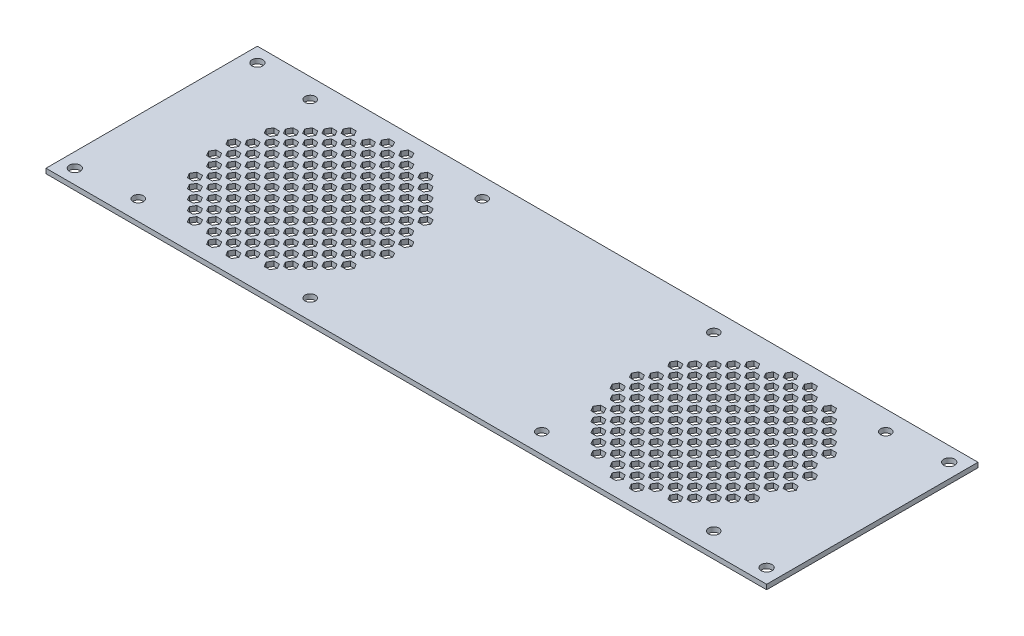
SolidWorks part; units mm, degrees
ref_plane "Front Plane" through (0, 0, 0) normal (0, 0, 1) x (1, 0, 0)
ref_plane "Top Plane" through (0, 0, 0) normal (0, 1, 0) x (1, 0, 0)
ref_plane "Right Plane" through (0, 0, 0) normal (1, 0, 0) x (0, 0, -1)
sketch "Sketch1" plane through (0, 0, 0) normal (0, 1, 0) x (1, 0, 0)
  line L1 (0, 0) -> (300, 0)
  line L2 (0, 0) -> (0, 88)
  line L3 (0, 88) -> (300, 88)
  line L4 (300, 0) -> (300, 88)
  dimension "D1" = 88
  dimension "D2" = 300
extrude "Boss-Extrude1" add sketch "Sketch1" along normal blind 2
hole_wizard "M4 Clearance Hole1" positions "Sketch2" profile "Sketch3" hole size "M4" standard "DIN" end condition up to next
sketch "Sketch2" plane through (0, 2, 0) normal (0, 1, 0) x (1, 0, 0)
  line L0 (0, 88) -> (0, 0) construction
  line L1 (0, 0) -> (300, 0) construction
  line L2 (300, 88) -> (0, 88) construction
  line L3 (300, 0) -> (300, 88) construction
  point P0 (294, 6)
  point P2 (294, 82)
  point P4 (6, 82)
  point P6 (6, 6)
  dimension "D1" = 6
  dimension "D2" = 6
  dimension "D3" = 6
  dimension "D4" = 6
sketch "Sketch3" plane through (294, 2, -6) normal (1, 0, 0) x (0, 0, 1)
  line L0 (0, 0) -> (0, 2)
  line L1 (0, 2) -> (2.25, 2)
  line L2 (2.25, 2) -> (2.25, 0)
  line L5 (2.25, 0) -> (0, 0)
  line L11 (0, -6.35) -> (0, 107.95) construction
  dimension "Thru Hole Dia." = 4.5
  dimension "Thru Hole Depth" = 2
sketch "Sketch4" plane through (0, 2, 0) normal (0, 1, 0) x (1, 0, 0)
  line L0 (0, 88) -> (0, 0) construction
  line L1 (68.3094, 44) -> (67.1547, 46)
  line L2 (67.1547, 46) -> (64.8453, 46)
  line L3 (64.8453, 46) -> (63.6906, 44)
  line L4 (63.6906, 44) -> (64.8453, 42)
  line L5 (64.8453, 42) -> (67.1547, 42)
  line L6 (67.1547, 42) -> (68.3094, 44)
  line L7 (76.3094, 44) -> (75.1547, 46)
  line L8 (75.1547, 46) -> (72.8453, 46)
  line L9 (72.8453, 46) -> (71.6906, 44)
  line L10 (71.6906, 44) -> (72.8453, 42)
  line L11 (72.8453, 42) -> (75.1547, 42)
  line L12 (75.1547, 42) -> (76.3094, 44)
  line L13 (84.3094, 44) -> (83.1547, 46)
  line L14 (83.1547, 46) -> (80.8453, 46)
  line L15 (80.8453, 46) -> (79.6906, 44)
  line L16 (79.6906, 44) -> (80.8453, 42)
  line L17 (80.8453, 42) -> (83.1547, 42)
  line L18 (83.1547, 42) -> (84.3094, 44)
  line L19 (92.3094, 44) -> (91.1547, 46)
  line L20 (91.1547, 46) -> (88.8453, 46)
  line L21 (88.8453, 46) -> (87.6906, 44)
  line L22 (87.6906, 44) -> (88.8453, 42)
  line L23 (88.8453, 42) -> (91.1547, 42)
  line L24 (91.1547, 42) -> (92.3094, 44)
  line L25 (100.3094, 44) -> (99.1547, 46)
  line L26 (99.1547, 46) -> (96.8453, 46)
  line L27 (96.8453, 46) -> (95.6906, 44)
  line L28 (95.6906, 44) -> (96.8453, 42)
  line L29 (96.8453, 42) -> (99.1547, 42)
  line L30 (99.1547, 42) -> (100.3094, 44)
  line L31 (76.3094, 52) -> (75.1547, 54)
  line L32 (75.1547, 54) -> (72.8453, 54)
  line L33 (72.8453, 54) -> (71.6906, 52)
  line L34 (71.6906, 52) -> (72.8453, 50)
  line L35 (72.8453, 50) -> (75.1547, 50)
  line L36 (75.1547, 50) -> (76.3094, 52)
  line L37 (84.3094, 52) -> (83.1547, 54)
  line L38 (83.1547, 54) -> (80.8453, 54)
  line L39 (80.8453, 54) -> (79.6906, 52)
  line L40 (79.6906, 52) -> (80.8453, 50)
  line L41 (80.8453, 50) -> (83.1547, 50)
  line L42 (83.1547, 50) -> (84.3094, 52)
  line L43 (92.3094, 52) -> (91.1547, 54)
  line L44 (91.1547, 54) -> (88.8453, 54)
  line L45 (88.8453, 54) -> (87.6906, 52)
  line L46 (87.6906, 52) -> (88.8453, 50)
  line L47 (88.8453, 50) -> (91.1547, 50)
  line L48 (91.1547, 50) -> (92.3094, 52)
  line L49 (100.3094, 52) -> (99.1547, 54)
  line L50 (99.1547, 54) -> (96.8453, 54)
  line L51 (96.8453, 54) -> (95.6906, 52)
  line L52 (95.6906, 52) -> (96.8453, 50)
  line L53 (96.8453, 50) -> (99.1547, 50)
  line L54 (99.1547, 50) -> (100.3094, 52)
  line L55 (76.3094, 60) -> (75.1547, 62)
  line L56 (75.1547, 62) -> (72.8453, 62)
  line L57 (72.8453, 62) -> (71.6906, 60)
  line L58 (71.6906, 60) -> (72.8453, 58)
  line L59 (72.8453, 58) -> (75.1547, 58)
  line L60 (75.1547, 58) -> (76.3094, 60)
  line L61 (84.3094, 60) -> (83.1547, 62)
  line L62 (83.1547, 62) -> (80.8453, 62)
  line L63 (80.8453, 62) -> (79.6906, 60)
  line L64 (79.6906, 60) -> (80.8453, 58)
  line L65 (80.8453, 58) -> (83.1547, 58)
  line L66 (83.1547, 58) -> (84.3094, 60)
  line L67 (92.3094, 60) -> (91.1547, 62)
  line L68 (91.1547, 62) -> (88.8453, 62)
  line L69 (88.8453, 62) -> (87.6906, 60)
  line L70 (87.6906, 60) -> (88.8453, 58)
  line L71 (88.8453, 58) -> (91.1547, 58)
  line L72 (91.1547, 58) -> (92.3094, 60)
  line L73 (100.3094, 60) -> (99.1547, 62)
  line L74 (99.1547, 62) -> (96.8453, 62)
  line L75 (96.8453, 62) -> (95.6906, 60)
  line L76 (95.6906, 60) -> (96.8453, 58)
  line L77 (96.8453, 58) -> (99.1547, 58)
  line L78 (99.1547, 58) -> (100.3094, 60)
  line L79 (76.3094, 68) -> (75.1547, 70)
  line L80 (75.1547, 70) -> (72.8453, 70)
  line L81 (72.8453, 70) -> (71.6906, 68)
  line L82 (71.6906, 68) -> (72.8453, 66)
  line L83 (72.8453, 66) -> (75.1547, 66)
  line L84 (75.1547, 66) -> (76.3094, 68)
  line L85 (84.3094, 68) -> (83.1547, 70)
  line L86 (83.1547, 70) -> (80.8453, 70)
  line L87 (80.8453, 70) -> (79.6906, 68)
  line L88 (79.6906, 68) -> (80.8453, 66)
  line L89 (80.8453, 66) -> (83.1547, 66)
  line L90 (83.1547, 66) -> (84.3094, 68)
  line L91 (92.3094, 68) -> (91.1547, 70)
  line L92 (91.1547, 70) -> (88.8453, 70)
  line L93 (88.8453, 70) -> (87.6906, 68)
  line L94 (87.6906, 68) -> (88.8453, 66)
  line L95 (88.8453, 66) -> (91.1547, 66)
  line L96 (91.1547, 66) -> (92.3094, 68)
  line L103 (76.3094, 76) -> (75.1547, 78)
  line L104 (75.1547, 78) -> (72.8453, 78)
  line L105 (72.8453, 78) -> (71.6906, 76)
  line L106 (71.6906, 76) -> (72.8453, 74)
  line L107 (72.8453, 74) -> (75.1547, 74)
  line L108 (75.1547, 74) -> (76.3094, 76)
  line L109 (84.3094, 76) -> (83.1547, 78)
  line L110 (83.1547, 78) -> (80.8453, 78)
  line L111 (80.8453, 78) -> (79.6906, 76)
  line L112 (79.6906, 76) -> (80.8453, 74)
  line L113 (80.8453, 74) -> (83.1547, 74)
  line L114 (83.1547, 74) -> (84.3094, 76)
  line L127 (68.3094, 52) -> (67.1547, 54)
  line L128 (67.1547, 54) -> (64.8453, 54)
  line L129 (64.8453, 54) -> (63.6906, 52)
  line L130 (63.6906, 52) -> (64.8453, 50)
  line L131 (64.8453, 50) -> (67.1547, 50)
  line L132 (67.1547, 50) -> (68.3094, 52)
  line L133 (68.3094, 60) -> (67.1547, 62)
  line L134 (67.1547, 62) -> (64.8453, 62)
  line L135 (64.8453, 62) -> (63.6906, 60)
  line L136 (63.6906, 60) -> (64.8453, 58)
  line L137 (64.8453, 58) -> (67.1547, 58)
  line L138 (67.1547, 58) -> (68.3094, 60)
  line L139 (68.3094, 68) -> (67.1547, 70)
  line L140 (67.1547, 70) -> (64.8453, 70)
  line L141 (64.8453, 70) -> (63.6906, 68)
  line L142 (63.6906, 68) -> (64.8453, 66)
  line L143 (64.8453, 66) -> (67.1547, 66)
  line L144 (67.1547, 66) -> (68.3094, 68)
  line L145 (68.3094, 76) -> (67.1547, 78)
  line L146 (67.1547, 78) -> (64.8453, 78)
  line L147 (64.8453, 78) -> (63.6906, 76)
  line L148 (63.6906, 76) -> (64.8453, 74)
  line L149 (64.8453, 74) -> (67.1547, 74)
  line L150 (67.1547, 74) -> (68.3094, 76)
  line L151 (92.3094, 76) -> (91.1547, 78) [skipped]
  line L152 (91.1547, 78) -> (88.8453, 78) [skipped]
  line L153 (88.8453, 78) -> (87.6906, 76) [skipped]
  line L154 (87.6906, 76) -> (88.8453, 74) [skipped]
  line L155 (88.8453, 74) -> (91.1547, 74) [skipped]
  line L156 (91.1547, 74) -> (92.3094, 76) [skipped]
  line L157 (100.3094, 76) -> (99.1547, 78) [skipped]
  line L158 (99.1547, 78) -> (96.8453, 78) [skipped]
  line L159 (96.8453, 78) -> (95.6906, 76) [skipped]
  line L160 (95.6906, 76) -> (96.8453, 74) [skipped]
  line L161 (96.8453, 74) -> (99.1547, 74) [skipped]
  line L162 (99.1547, 74) -> (100.3094, 76) [skipped]
  line L163 (100.3094, 68) -> (99.1547, 70) [skipped]
  line L164 (99.1547, 70) -> (96.8453, 70) [skipped]
  line L165 (96.8453, 70) -> (95.6906, 68) [skipped]
  line L166 (95.6906, 68) -> (96.8453, 66) [skipped]
  line L167 (96.8453, 66) -> (99.1547, 66) [skipped]
  line L168 (99.1547, 66) -> (100.3094, 68) [skipped]
  circle A0 centre (66, 44) radius 2 construction
  point P11 (0, 44)
  dimension "D2" = 4
  dimension "D1" = 66
  dimension "D5" = 8
  dimension "D6" = 8
  dimension "D3" = 5
  dimension "D4" = 5
extrude "Cut-Extrude1" cut sketch "Sketch4" against normal up to next (2 mm away)
sketch "Sketch5" plane through (0, 2, 0) normal (0, 1, 0) x (1, 0, 0)
  line L0 (67.1547, 46) -> (64.8453, 46) construction
  line L1 (72.3094, 48) -> (71.1547, 50)
  line L2 (71.1547, 50) -> (68.8453, 50)
  line L3 (68.8453, 50) -> (67.6906, 48)
  line L4 (67.6906, 48) -> (68.8453, 46)
  line L5 (68.8453, 46) -> (71.1547, 46)
  line L6 (71.1547, 46) -> (72.3094, 48)
  line L7 (64.8453, 42) -> (67.1547, 42) construction
  line L8 (80.3094, 48) -> (79.1547, 50)
  line L9 (79.1547, 50) -> (76.8453, 50)
  line L10 (76.8453, 50) -> (75.6906, 48)
  line L11 (75.6906, 48) -> (76.8453, 46)
  line L12 (76.8453, 46) -> (79.1547, 46)
  line L13 (79.1547, 46) -> (80.3094, 48)
  line L14 (88.3094, 48) -> (87.1547, 50)
  line L15 (87.1547, 50) -> (84.8453, 50)
  line L16 (84.8453, 50) -> (83.6906, 48)
  line L17 (83.6906, 48) -> (84.8453, 46)
  line L18 (84.8453, 46) -> (87.1547, 46)
  line L19 (87.1547, 46) -> (88.3094, 48)
  line L20 (96.3094, 48) -> (95.1547, 50)
  line L21 (95.1547, 50) -> (92.8453, 50)
  line L22 (92.8453, 50) -> (91.6906, 48)
  line L23 (91.6906, 48) -> (92.8453, 46)
  line L24 (92.8453, 46) -> (95.1547, 46)
  line L25 (95.1547, 46) -> (96.3094, 48)
  line L26 (104.3094, 48) -> (103.1547, 50)
  line L27 (103.1547, 50) -> (100.8453, 50)
  line L28 (100.8453, 50) -> (99.6906, 48)
  line L29 (99.6906, 48) -> (100.8453, 46)
  line L30 (100.8453, 46) -> (103.1547, 46)
  line L31 (103.1547, 46) -> (104.3094, 48)
  line L32 (80.3094, 56) -> (79.1547, 58)
  line L33 (79.1547, 58) -> (76.8453, 58)
  line L34 (76.8453, 58) -> (75.6906, 56)
  line L35 (75.6906, 56) -> (76.8453, 54)
  line L36 (76.8453, 54) -> (79.1547, 54)
  line L37 (79.1547, 54) -> (80.3094, 56)
  line L38 (88.3094, 56) -> (87.1547, 58)
  line L39 (87.1547, 58) -> (84.8453, 58)
  line L40 (84.8453, 58) -> (83.6906, 56)
  line L41 (83.6906, 56) -> (84.8453, 54)
  line L42 (84.8453, 54) -> (87.1547, 54)
  line L43 (87.1547, 54) -> (88.3094, 56)
  line L44 (96.3094, 56) -> (95.1547, 58)
  line L45 (95.1547, 58) -> (92.8453, 58)
  line L46 (92.8453, 58) -> (91.6906, 56)
  line L47 (91.6906, 56) -> (92.8453, 54)
  line L48 (92.8453, 54) -> (95.1547, 54)
  line L49 (95.1547, 54) -> (96.3094, 56)
  line L56 (80.3094, 64) -> (79.1547, 66)
  line L57 (79.1547, 66) -> (76.8453, 66)
  line L58 (76.8453, 66) -> (75.6906, 64)
  line L59 (75.6906, 64) -> (76.8453, 62)
  line L60 (76.8453, 62) -> (79.1547, 62)
  line L61 (79.1547, 62) -> (80.3094, 64)
  line L62 (88.3094, 64) -> (87.1547, 66)
  line L63 (87.1547, 66) -> (84.8453, 66)
  line L64 (84.8453, 66) -> (83.6906, 64)
  line L65 (83.6906, 64) -> (84.8453, 62)
  line L66 (84.8453, 62) -> (87.1547, 62)
  line L67 (87.1547, 62) -> (88.3094, 64)
  line L68 (96.3094, 64) -> (95.1547, 66)
  line L69 (95.1547, 66) -> (92.8453, 66)
  line L70 (92.8453, 66) -> (91.6906, 64)
  line L71 (91.6906, 64) -> (92.8453, 62)
  line L72 (92.8453, 62) -> (95.1547, 62)
  line L73 (95.1547, 62) -> (96.3094, 64)
  line L80 (80.3094, 72) -> (79.1547, 74)
  line L81 (79.1547, 74) -> (76.8453, 74)
  line L82 (76.8453, 74) -> (75.6906, 72)
  line L83 (75.6906, 72) -> (76.8453, 70)
  line L84 (76.8453, 70) -> (79.1547, 70)
  line L85 (79.1547, 70) -> (80.3094, 72)
  line L86 (88.3094, 72) -> (87.1547, 74)
  line L87 (87.1547, 74) -> (84.8453, 74)
  line L88 (84.8453, 74) -> (83.6906, 72)
  line L89 (83.6906, 72) -> (84.8453, 70)
  line L90 (84.8453, 70) -> (87.1547, 70)
  line L91 (87.1547, 70) -> (88.3094, 72)
  line L128 (72.3094, 56) -> (71.1547, 58)
  line L129 (71.1547, 58) -> (68.8453, 58)
  line L130 (68.8453, 58) -> (67.6906, 56)
  line L131 (67.6906, 56) -> (68.8453, 54)
  line L132 (68.8453, 54) -> (71.1547, 54)
  line L133 (71.1547, 54) -> (72.3094, 56)
  line L134 (72.3094, 64) -> (71.1547, 66)
  line L135 (71.1547, 66) -> (68.8453, 66)
  line L136 (68.8453, 66) -> (67.6906, 64)
  line L137 (67.6906, 64) -> (68.8453, 62)
  line L138 (68.8453, 62) -> (71.1547, 62)
  line L139 (71.1547, 62) -> (72.3094, 64)
  line L140 (72.3094, 72) -> (71.1547, 74)
  line L141 (71.1547, 74) -> (68.8453, 74)
  line L142 (68.8453, 74) -> (67.6906, 72)
  line L143 (67.6906, 72) -> (68.8453, 70)
  line L144 (68.8453, 70) -> (71.1547, 70)
  line L145 (71.1547, 70) -> (72.3094, 72)
  line L146 (72.3094, 80) -> (71.1547, 82)
  line L147 (71.1547, 82) -> (68.8453, 82)
  line L148 (68.8453, 82) -> (67.6906, 80)
  line L149 (67.6906, 80) -> (68.8453, 78)
  line L150 (68.8453, 78) -> (71.1547, 78)
  line L151 (71.1547, 78) -> (72.3094, 80)
  line L152 (96.3094, 72) -> (95.1547, 74) [skipped]
  line L153 (95.1547, 74) -> (92.8453, 74) [skipped]
  line L154 (92.8453, 74) -> (91.6906, 72) [skipped]
  line L155 (91.6906, 72) -> (92.8453, 70) [skipped]
  line L156 (92.8453, 70) -> (95.1547, 70) [skipped]
  line L157 (95.1547, 70) -> (96.3094, 72) [skipped]
  line L158 (103.1547, 70) -> (104.3094, 72) [skipped]
  line L159 (104.3094, 72) -> (103.1547, 74) [skipped]
  line L160 (103.1547, 74) -> (100.8453, 74) [skipped]
  line L161 (100.8453, 74) -> (99.6906, 72) [skipped]
  line L162 (99.6906, 72) -> (100.8453, 70) [skipped]
  line L163 (100.8453, 70) -> (103.1547, 70) [skipped]
  line L164 (104.3094, 80) -> (103.1547, 82) [skipped]
  line L165 (103.1547, 82) -> (100.8453, 82) [skipped]
  line L166 (100.8453, 82) -> (99.6906, 80) [skipped]
  line L167 (99.6906, 80) -> (100.8453, 78) [skipped]
  line L168 (100.8453, 78) -> (103.1547, 78) [skipped]
  line L169 (103.1547, 78) -> (104.3094, 80) [skipped]
  line L170 (96.3094, 80) -> (95.1547, 82) [skipped]
  line L171 (95.1547, 82) -> (92.8453, 82) [skipped]
  line L172 (92.8453, 82) -> (91.6906, 80) [skipped]
  line L173 (91.6906, 80) -> (92.8453, 78) [skipped]
  line L174 (92.8453, 78) -> (95.1547, 78) [skipped]
  line L175 (95.1547, 78) -> (96.3094, 80) [skipped]
  line L176 (104.3094, 64) -> (103.1547, 66) [skipped]
  line L177 (103.1547, 66) -> (100.8453, 66) [skipped]
  line L178 (100.8453, 66) -> (99.6906, 64) [skipped]
  line L179 (99.6906, 64) -> (100.8453, 62) [skipped]
  line L180 (100.8453, 62) -> (103.1547, 62) [skipped]
  line L181 (103.1547, 62) -> (104.3094, 64) [skipped]
  line L182 (104.3094, 56) -> (103.1547, 58) [skipped]
  line L183 (103.1547, 58) -> (100.8453, 58) [skipped]
  line L184 (100.8453, 58) -> (99.6906, 56) [skipped]
  line L185 (99.6906, 56) -> (100.8453, 54) [skipped]
  line L186 (100.8453, 54) -> (103.1547, 54) [skipped]
  line L187 (103.1547, 54) -> (104.3094, 56) [skipped]
  line L188 (88.3094, 80) -> (87.1547, 82) [skipped]
  line L189 (87.1547, 82) -> (84.8453, 82) [skipped]
  line L190 (84.8453, 82) -> (83.6906, 80) [skipped]
  line L191 (83.6906, 80) -> (84.8453, 78) [skipped]
  line L192 (84.8453, 78) -> (87.1547, 78) [skipped]
  line L193 (87.1547, 78) -> (88.3094, 80) [skipped]
  line L194 (80.3094, 80) -> (79.1547, 82) [skipped]
  line L195 (79.1547, 82) -> (76.8453, 82) [skipped]
  line L196 (76.8453, 82) -> (75.6906, 80) [skipped]
  line L197 (75.6906, 80) -> (76.8453, 78) [skipped]
  line L198 (76.8453, 78) -> (79.1547, 78) [skipped]
  line L199 (79.1547, 78) -> (80.3094, 80) [skipped]
  circle A0 centre (70, 48) radius 2 construction
  point P13 (66, 42)
  dimension "D1" = 4
  dimension "D2" = 4
  dimension "D5" = 8
  dimension "D6" = 8
  dimension "D3" = 5
  dimension "D4" = 5
extrude "Cut-Extrude2" cut sketch "Sketch5" against normal up to next (2 mm away)
ref_plane "Plane1" through (66, 0, 0) normal (-1, 0, 0) x (0, 0, 1)
ref_plane "Plane2" through (0, 0, -44) normal (0, 0, -1) x (-1, 0, 0)
mirror "Mirror1" about plane through (66, 0, 0) normal (-1, 0, 0) of "Cut-Extrude2", "Cut-Extrude1"
mirror "Mirror2" about plane through (0, 0, -44) normal (0, 0, -1) of "Mirror1", "Cut-Extrude1", "Cut-Extrude2"
ref_plane "Plane3" through (150, 0, 0) normal (-1, 0, 0) x (0, 0, 1)
mirror "Mirror3" about plane through (150, 0, 0) normal (-1, 0, 0) of "Mirror2", "Cut-Extrude1", "Cut-Extrude2", "Mirror1"
hole_wizard "M4 Clearance Hole2" positions "Sketch8" profile "Sketch7" hole size "M4" standard "DIN"
sketch "Sketch8" plane through (0, 2, 0) normal (0, 1, 0) x (1, 0, 0)
  line L1 (30.2, 8.2) -> (101.8, 8.2) construction
  line L2 (30.2, 8.2) -> (30.2, 79.8) construction
  line L3 (30.2, 79.8) -> (101.8, 79.8) construction
  line L4 (101.8, 8.2) -> (101.8, 79.8) construction
  line L5 (30.2, 8.2) -> (101.8, 79.8) construction
  line L6 (30.2, 79.8) -> (101.8, 8.2) construction
  line L7 (67.1547, 46) -> (64.8453, 46) construction
  line L9 (198.2, 8.2) -> (269.8, 8.2) construction
  line L10 (198.2, 8.2) -> (198.2, 79.8) construction
  line L11 (198.2, 79.8) -> (269.8, 79.8) construction
  line L12 (269.8, 8.2) -> (269.8, 79.8) construction
  line L13 (198.2, 8.2) -> (269.8, 79.8) construction
  line L14 (198.2, 79.8) -> (269.8, 8.2) construction
  line L15 (232.8453, 46) -> (235.1547, 46) construction
  point P2 (101.8, 79.8)
  point P101 (30.2, 8.2)
  point P102 (30.2, 79.8)
  point P103 (101.8, 8.2)
  point P109 (66, 44)
  point P112 (66, 46)
  point P114 (269.8, 79.8)
  point P197 (198.2, 8.2)
  point P198 (198.2, 79.8)
  point P199 (269.8, 8.2)
  point P202 (234, 44)
  point P205 (234, 46)
  dimension "D1" = 71.6
sketch "Sketch7" plane through (101.8, 2, -79.8) normal (1, 0, 0) x (0, 0, 1)
  line L0 (0, 0) -> (0, 2)
  line L1 (0, 2) -> (2.15, 2)
  line L2 (2.15, 2) -> (2.15, 0)
  line L5 (2.15, 0) -> (0, 0)
  line L11 (0, -6.35) -> (0, 107.95) construction
  dimension "Thru Hole Dia." = 4.3
  dimension "Thru Hole Depth" = 2
